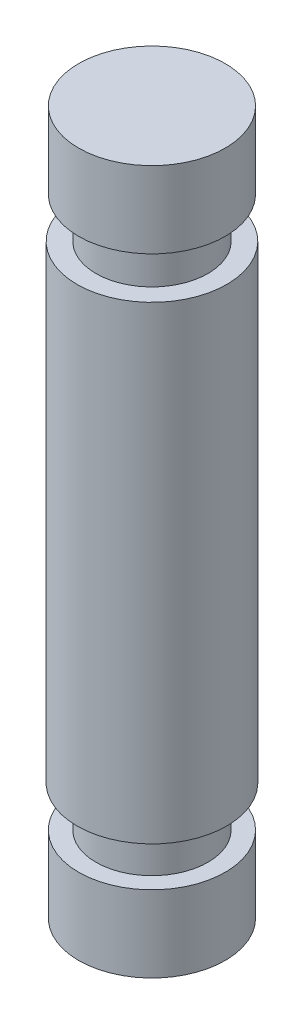
SolidWorks part; units mm, degrees
material "AISI 1020"
ref_plane "Front Plane" through (0, 0, 0) normal (0, 0, 1) x (1, 0, 0)
ref_plane "Top Plane" through (0, 0, 0) normal (0, 1, 0) x (1, 0, 0)
ref_plane "Right Plane" through (0, 0, 0) normal (1, 0, 0) x (0, 0, -1)
sketch "Sketch2" plane through (0, 0, 0) normal (0, 1, 0) x (1, 0, 0)
  circle A0 centre (0, 0) radius 3.5
  dimension "D1" = 7
extrude "Boss-Extrude1" add sketch "Sketch2" along normal blind 3.65
sketch "Sketch3" plane through (0, 3.65, 0) normal (0, 1, 0) x (1, 0, 0)
  circle A0 centre (0, 0) radius 2.675
  dimension "D1" = 5.35
extrude "Boss-Extrude2" add sketch "Sketch3" along normal blind 1.95
sketch "Sketch4" plane through (0, 5.6, 0) normal (0, 1, 0) x (1, 0, 0)
  circle A0 centre (0, 0) radius 3.575
  dimension "D1" = 7.15
extrude "Boss-Extrude3" add sketch "Sketch4" along normal blind 22.4
sketch "Sketch5" plane through (0, 28, 0) normal (0, 1, 0) x (1, 0, 0)
  circle A0 centre (0, 0) radius 2.675
  dimension "D1" = 5.35
extrude "Boss-Extrude4" add sketch "Sketch5" along normal blind 1.95
sketch "Sketch6" plane through (0, 29.95, 0) normal (0, 1, 0) x (1, 0, 0)
  circle A0 centre (0, 0) radius 3.5
  dimension "D1" = 7
extrude "Boss-Extrude5" add sketch "Sketch6" along normal blind 3.65
